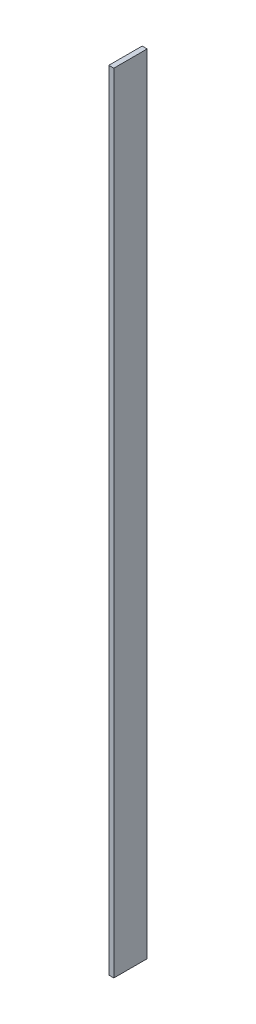
SolidWorks part; units mm, degrees
ref_plane "Front Plane" through (0, 0, 0) normal (0, 0, 1) x (1, 0, 0)
ref_plane "Top Plane" through (0, 0, 0) normal (0, 1, 0) x (1, 0, 0)
ref_plane "Right Plane" through (0, 0, 0) normal (1, 0, 0) x (0, 0, -1)
sketch "Sketch1" plane through (0, 0, 0) normal (1, 0, 0) x (0, 0, -1)
  line L1 (0, 0) -> (15.875, 0)
  line L2 (0, 0) -> (0, 374.65)
  line L3 (0, 374.65) -> (15.875, 374.65)
  line L4 (15.875, 0) -> (15.875, 374.65)
  dimension "D1" = 374.65
  dimension "D2" = 15.875
extrude "Boss-Extrude1" add sketch "Sketch1" along normal blind 2.3813
